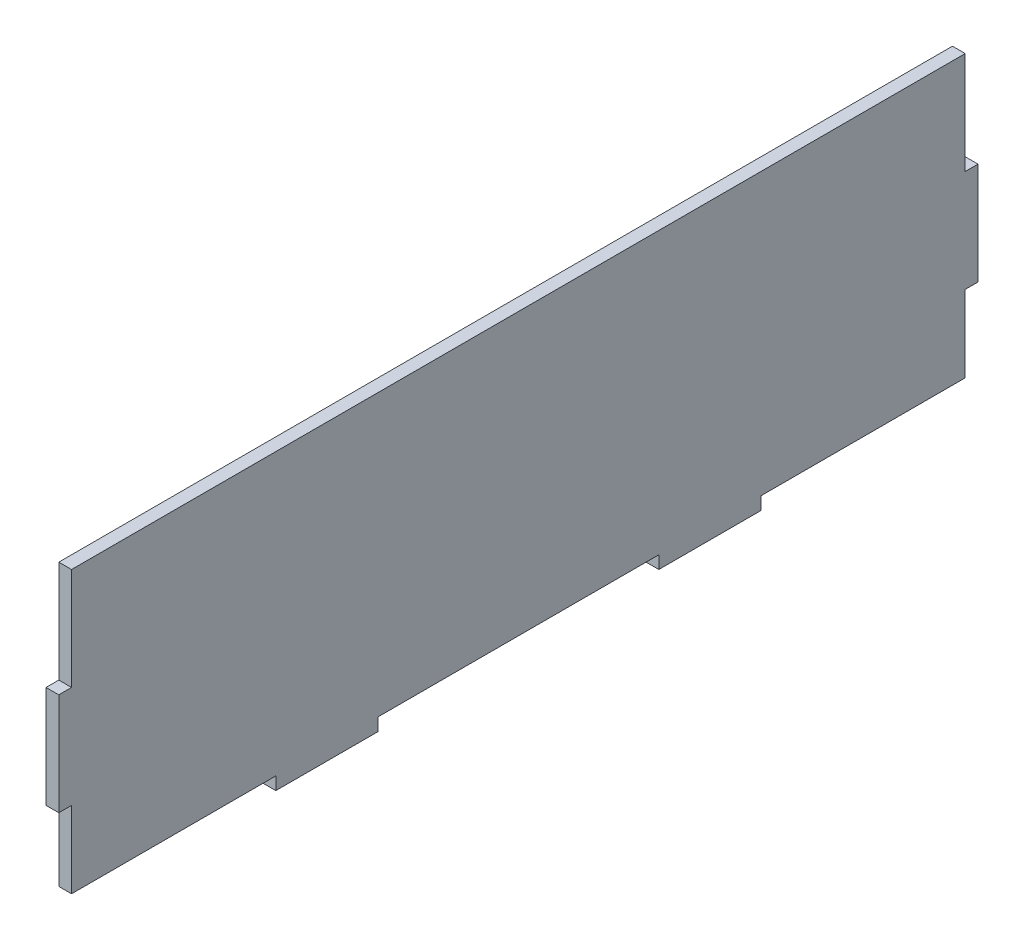
SolidWorks part; units mm, degrees
ref_plane "Front Plane" through (0, 0, 0) normal (0, 0, 1) x (1, 0, 0)
ref_plane "Top Plane" through (0, 0, 0) normal (0, 1, 0) x (1, 0, 0)
ref_plane "Right Plane" through (0, 0, 0) normal (1, 0, 0) x (0, 0, -1)
sketch "Sketch1" plane through (0, 0, 0) normal (1, 0, 0) x (0, 0, -1)
  line L0 (-116.66, 27.079) -> (-116.66, 1.679)
  line L1 (-116.66, 27.079) -> (105.59, 27.079)
  line L2 (-116.66, 1.679) -> (-119.835, 1.679)
  line L3 (-116.66, -42.771) -> (-65.86, -42.771)
  line L4 (-119.835, 1.679) -> (-119.835, -23.721)
  line L5 (-119.835, -23.721) -> (-116.66, -23.721)
  line L6 (-116.66, -23.721) -> (-116.66, -42.771)
  line L7 (105.59, 27.079) -> (105.59, 1.679)
  line L8 (105.59, 1.679) -> (108.765, 1.679)
  line L9 (108.765, 1.679) -> (108.765, -23.721)
  line L10 (108.765, -23.721) -> (105.59, -23.721)
  line L11 (105.59, -23.721) -> (105.59, -42.771)
  line L12 (-65.86, -42.771) -> (-65.86, -45.946)
  line L13 (-65.86, -45.946) -> (-40.46, -45.946)
  line L14 (-40.46, -45.946) -> (-40.46, -42.771)
  line L15 (-40.46, -42.771) -> (29.39, -42.771)
  line L16 (29.39, -42.771) -> (29.39, -45.946)
  line L17 (29.39, -45.946) -> (54.79, -45.946)
  line L18 (54.79, -45.946) -> (54.79, -42.771)
  line L19 (54.79, -42.771) -> (105.59, -42.771)
  dimension "D1" = 222.25
  dimension "D2" = 25.4
  dimension "D3" = 25.4
  dimension "D4" = 3.175
  dimension "D5" = 3.175
  dimension "D6" = 3.175
  dimension "D7" = 19.05
  dimension "D8" = 25.4
  dimension "D9" = 25.4
  dimension "D10" = 50.8
  dimension "D11" = 50.8
  dimension "D12" = 3.175
  dimension "D13" = 69.85
  dimension "D14" = 3.175
  dimension "D15" = 3.175
  dimension "D16" = 3.175
  dimension "D17" = 25.4
  dimension "D18" = 25.4
extrude "Boss-Extrude1" add sketch "Sketch1" along normal blind 3.175
